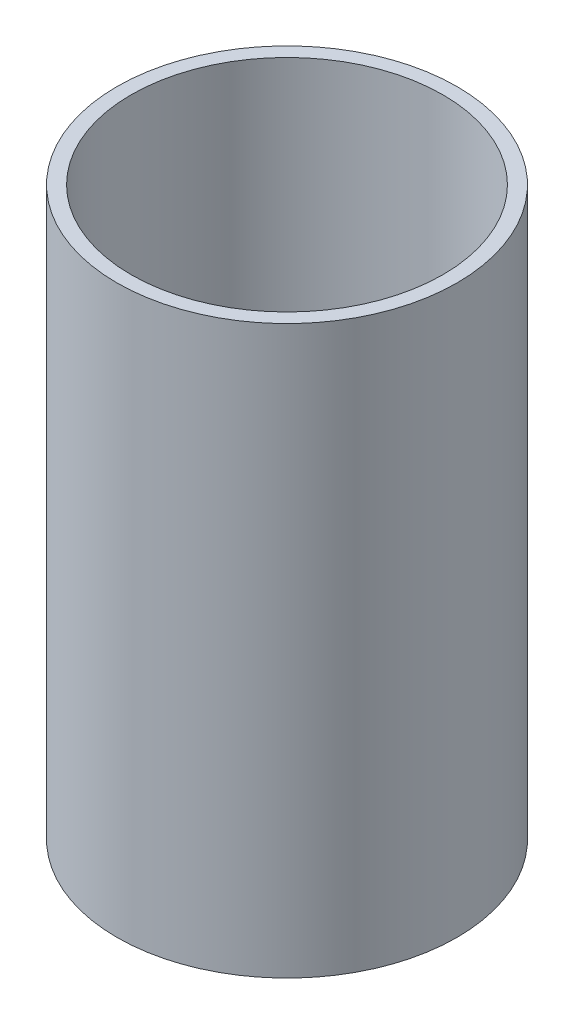
SolidWorks part; units mm, degrees
ref_plane "Front Plane" through (0, 0, 0) normal (0, 0, 1) x (1, 0, 0)
ref_plane "Top Plane" through (0, 0, 0) normal (0, 1, 0) x (1, 0, 0)
ref_plane "Right Plane" through (0, 0, 0) normal (1, 0, 0) x (0, 0, -1)
sketch "Sketch2" plane through (0, 0, 0) normal (0, 1, 0) x (1, 0, 0)
  circle A0 centre (0, 0) radius 38.1
  dimension "D1" = 76.2
extrude "Boss-Extrude1" add sketch "Sketch2" along normal blind 127
sketch "Sketch3" plane through (0, 127, 0) normal (0, 1, 0) x (1, 0, 0)
  circle A0 centre (0, 0) radius 34.925
  dimension "D1" = 69.85
extrude "Cut-Extrude1" cut sketch "Sketch3" against normal blind 127
